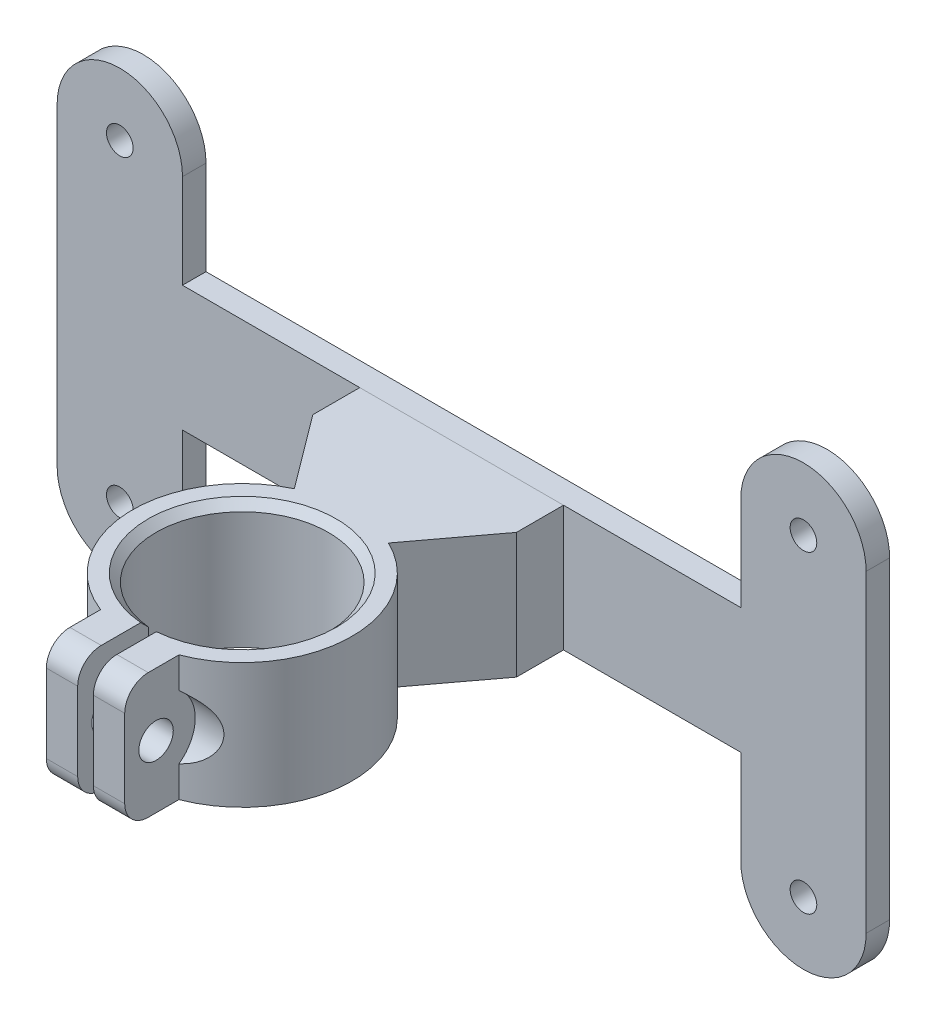
SolidWorks part; units mm, degrees
other "abrazadera"
other "cople"
ref_plane "Front Plane" through (0, 0, 0) normal (0, 0, 1) x (1, 0, 0)
ref_plane "Top Plane" through (0, 0, 0) normal (0, 1, 0) x (1, 0, 0)
ref_plane "Right Plane" through (0, 0, 0) normal (1, 0, 0) x (0, 0, -1)
sketch "Sketch1" plane through (0, 0, 0) normal (0, 0, 1) x (1, 0, 0)
  line L0 (-43.625, 20) -> (-43.625, -20) construction
  line L1 (-43.625, -20) -> (43.625, -20) construction
  line L2 (-43.625, -20) -> (-43.625, 20) construction
  line L3 (-43.625, 20) -> (43.625, 20) construction
  line L4 (43.625, -20) -> (43.625, 20) construction
  line L5 (-43.625, -20) -> (43.625, 20) construction
  line L6 (-43.625, 20) -> (43.625, -20) construction
  line L7 (-35.625, 20) -> (-35.625, -20)
  line L8 (-51.625, 20) -> (-51.625, -20)
  line L9 (43.625, 20) -> (43.625, -20) construction
  line L10 (51.625, 20) -> (51.625, -20)
  line L11 (35.625, 20) -> (35.625, -20)
  line L12 (-43.625, 0) -> (43.625, 0) construction
  line L13 (-43.625, 8) -> (43.625, 8)
  line L14 (-43.625, -8) -> (43.625, -8)
  arc A0 (-35.625, 20) -> (-51.625, 20) centre (-43.625, 20) ccw
  arc A1 (-51.625, -20) -> (-35.625, -20) centre (-43.625, -20) ccw
  arc A2 (51.625, 20) -> (35.625, 20) centre (43.625, 20) ccw
  arc A3 (35.625, -20) -> (51.625, -20) centre (43.625, -20) ccw
  arc A4 (-43.625, 8) -> (-43.625, -8) centre (-43.625, 0) ccw
  arc A5 (43.625, -8) -> (43.625, 8) centre (43.625, 0) ccw
  circle A6 centre (-43.625, 20) radius 1.7
  circle A7 centre (43.625, 20) radius 1.7
  circle A8 centre (43.625, -20) radius 1.7
  circle A9 centre (-43.625, -20) radius 1.7
  point P0 (0, 0)
  point P6 (-43.625, 0)
  point P11 (43.625, 0)
  point P16 (0, 0)
  dimension "D3" = 3.4
  dimension "D1" = 40
  dimension "D2" = 87.25
  dimension "D4" = 16
  dimension "D5" = 16
  dimension "D6" = 16
extrude "Boss-Extrude1" add sketch "Sketch1" along normal blind 3 contours A4 L13 L7 A0 L8 A6 | A4 L8 A1 L7 L14 A9 | L7 L14 L11 L13 | L13 A4 L14 L7 | A5 L13 L11 L14 | A5 L10 A2 L11 L13 A7 | A5 L14 L11 A3 L10 A8
sketch "Sketch2" plane through (0, -8, 0) normal (0, -1, 0) x (1, 0, 0)
  line L0 (0, 0) -> (0, 6) construction
  line L1 (-10, 6) -> (10, 6)
  line L2 (10, 6) -> (7.5, 3)
  line L3 (-35.625, 3) -> (35.625, 3) construction
  line L4 (7.5, 3) -> (-7.5, 3)
  line L5 (-7.5, 3) -> (-10, 6)
  point P3 (0, 6)
  point P10 (0, 0)
  point P11 (0, 3)
  dimension "D1" = 20
  dimension "D2" = 15
  dimension "D3" = 3
extrude "Boss-Extrude2" add sketch "Sketch2" against normal blind 13
sketch "Sketch5" plane through (0, 8, 0) normal (0, 1, 0) x (1, 0, 0)
  line L0 (-35.625, -3) -> (35.625, -3) construction
  line L1 (-13, -3) -> (13, -3)
  line L2 (-13, -3) -> (-13, -9)
  line L4 (13, -3) -> (13, -9)
  line L5 (0, -31) -> (0, 0) construction
  line L6 (-13, -9) -> (13, -9) construction
  line L7 (13, -9) -> (6, -18.3509)
  line L8 (-6, -18.3509) -> (6, -18.3509) construction
  line L9 (-6, -18.3509) -> (-13, -9)
  line L10 (10, -6) -> (-10, -6) construction
  circle A0 centre (0, -31) radius 11
  arc A1 (-6, -18.3509) -> (6, -18.3509) centre (0, -31) ccw
  circle A2 centre (0, -31) radius 14 construction
  point P12 (0, -20)
  dimension "D1" = 22
  dimension "D3" = 3
  dimension "D4" = 3
  dimension "D5" = 20
  dimension "D6" = 3
  dimension "D7" = 12
  dimension "D2" = 3
extrude "Boss-Extrude3" add sketch "Sketch5" against normal blind 16 separate body
sketch "Sketch6" plane through (0, 8, 0) normal (0, 1, 0) x (1, 0, 0)
  line L0 (0, -31) -> (0, -45) construction
  line L1 (-5, -31) -> (5, -31)
  line L2 (-5, -31) -> (-5, -51)
  line L3 (-5, -51) -> (5, -51)
  line L4 (5, -31) -> (5, -51)
  circle A0 centre (0, -31) radius 11 construction
  arc A1 (-6, -18.3509) -> (6, -18.3509) centre (0, -31) ccw construction
  point P4 (0, -31)
  arc M8 (-6, -18.3509) -> (6, -18.3509) centre (0, -31) ccw
  dimension "D1" = 10
  dimension "D2" = 6
  dimension "D3" = 20
extrude "Boss-Extrude4" add sketch "Sketch6" against normal blind 16 contours L4 L2 L3 M8
sketch "Sketch7" plane through (0, 8, 0) normal (0, 1, 0) x (1, 0, 0)
  line L0 (-5, -51) -> (5, -51) construction
  line L1 (-1, -39) -> (1, -39)
  line L2 (-1, -39) -> (-1, -51)
  line L3 (-1, -51) -> (1, -51)
  line L4 (1, -39) -> (1, -51)
  point P6 (0, -51)
  point P7 (0, -51)
  dimension "D1" = 2
  dimension "D2" = 12
extrude "Cut-Extrude1" cut sketch "Sketch7" against normal through all
sketch "Sketch8" plane through (-5, 0, 0) normal (-1, 0, 0) x (0, 0, 1)
  line L0 (0, 0) -> (47, 0) construction
  line L1 (51, -8) -> (51, 8) construction
  line L2 (47, 0) -> (49.2, 0) construction
  line L3 (49.2, 0) -> (51, 0) construction
  circle A0 centre (47, 0) radius 2.2
  dimension "D1" = 4.4
  dimension "D2" = 4
  dimension "D3" = 1.8
  dimension "D4" = 4
extrude "Cut-Extrude2" cut sketch "Sketch8" against normal blind 15 and the other way blind 5
sketch "Sketch9" plane through (-5, 0, 0) normal (-1, 0, 0) x (0, 0, 1)
  circle A0 centre (47, 0) radius 5
  dimension "D1" = 10
extrude "Cut-Extrude3" cut sketch "Sketch9" along normal blind 5
mirror "Mirror1" about plane through (0, 0, 0) normal (1, 0, 0) of "Cut-Extrude3"
sketch "Sketch10" plane through (0, -8, 0) normal (0, -1, 0) x (1, 0, 0)
  line L0 (-7.6536, 2.872) -> (7.6536, 2.872)
  line L19 (10.427, 6.2) -> (-10.427, 6.2)
  line L20 (7.6536, 2.872) -> (10.427, 6.2)
  line L21 (-10.427, 6.2) -> (-7.6536, 2.872)
  line L22 (10.427, 6.2) -> (-10.427, 6.2)
  line L23 (7.6536, 2.872) -> (10.427, 6.2)
  line L24 (-10.427, 6.2) -> (-7.6536, 2.872)
  dimension "D1" = 0.2
extrude "Cut-Extrude4" cut sketch "Sketch10" against normal blind 13.5 contours L22 L24 L0 L23
fillet "Fillet1" radius 3 4 edges at (3, -8, 51) (-3, -8, 51) (3, 8, 51) (-3, 8, 51)
chamfer "Chamfer1" distance 1 angle 45 1 edges at (0, 8, 20)
